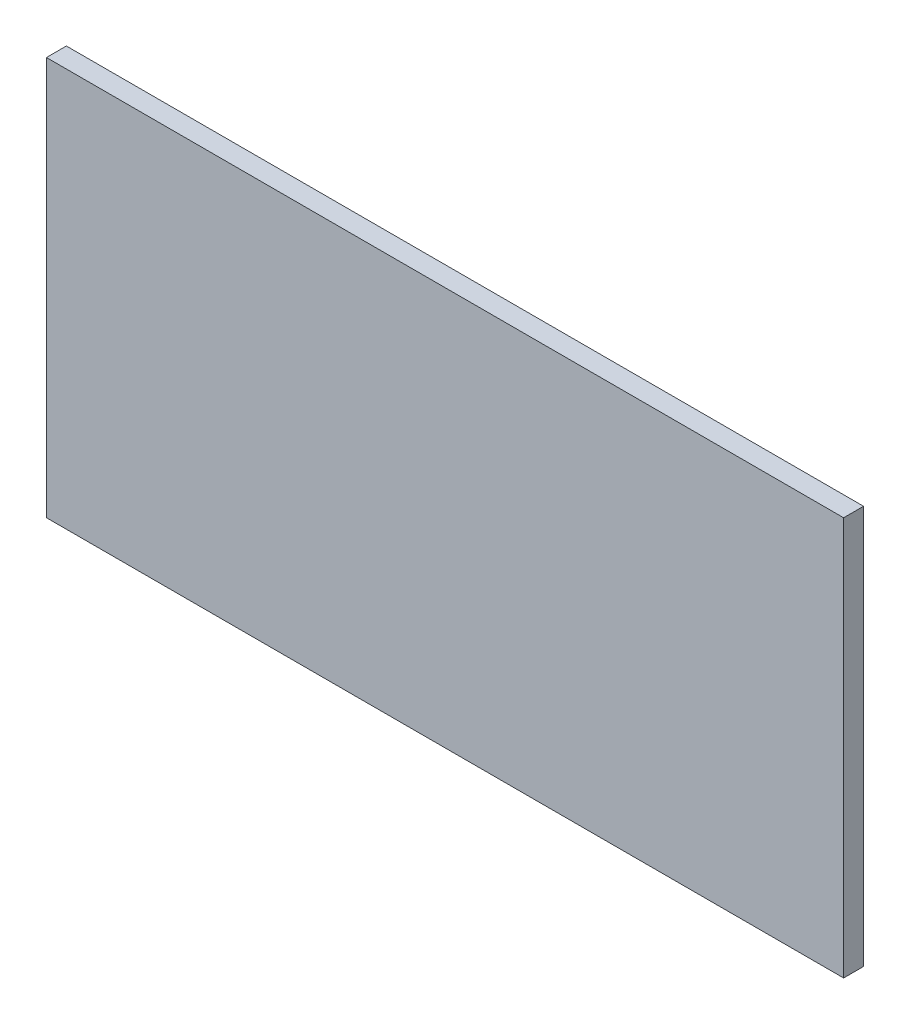
SolidWorks part; units mm, degrees
ref_plane "Front Plane" through (0, 0, 0) normal (0, 0, 1) x (1, 0, 0)
ref_plane "Top Plane" through (0, 0, 0) normal (0, 1, 0) x (1, 0, 0)
ref_plane "Right Plane" through (0, 0, 0) normal (1, 0, 0) x (0, 0, -1)
sketch "Sketch1" plane through (0, 0, 0) normal (0, 0, 1) x (1, 0, 0)
  line L1 (100, -50) -> (-100, -50)
  line L2 (100, -50) -> (100, 50)
  line L3 (100, 50) -> (-100, 50)
  line L4 (-100, -50) -> (-100, 50)
  line L5 (100, -50) -> (-100, 50) construction
  line L6 (100, 50) -> (-100, -50) construction
  point P0 (0, 0)
  dimension "D1" = 100
  dimension "D2" = 200
extrude "Boss-Extrude1" add sketch "Sketch1" along normal blind 5
